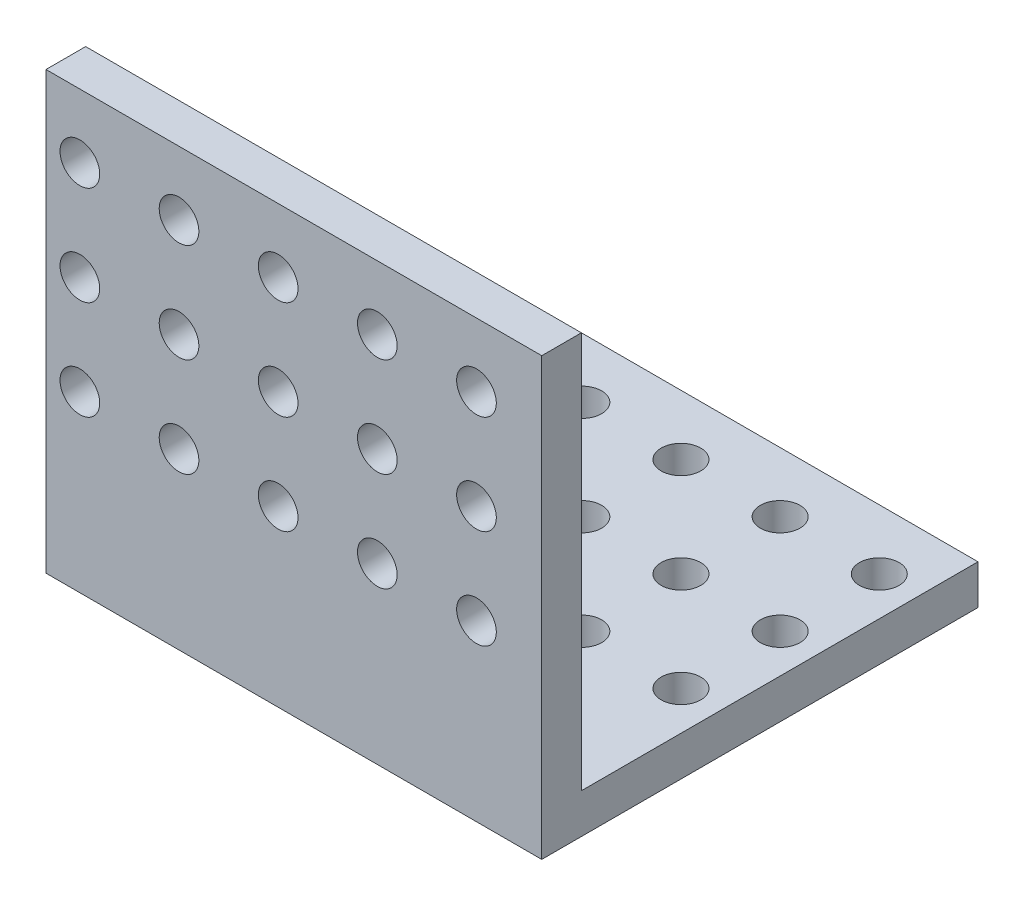
SolidWorks part; units mm, degrees
ref_plane "Front Plane" through (0, 0, 0) normal (0, 0, 1) x (1, 0, 0)
ref_plane "Top Plane" through (0, 0, 0) normal (0, 1, 0) x (1, 0, 0)
ref_plane "Right Plane" through (0, 0, 0) normal (1, 0, 0) x (0, 0, -1)
sketch "Sketch1" plane through (0, 0, 0) normal (1, 0, 0) x (0, 0, -1)
  line L0 (0, 40) -> (0, 0)
  line L1 (0, 0) -> (40, 0)
  dimension "D1" = 40
  dimension "D2" = 40
extrude "Extrude-Thin1" add sketch "Sketch1" along normal mid plane 50 thin
sketch "Sketch2" plane through (0, 0, 0) normal (0, 1, 0) x (1, 0, 0)
  circle A0 centre (-18.9109, 33.9533) radius 2
  circle A1 centre (-8.9109, 33.9533) radius 2
  circle A2 centre (1.0891, 33.9533) radius 2
  circle A3 centre (11.0891, 33.9533) radius 2
  circle A4 centre (21.0891, 33.9533) radius 2
  circle A5 centre (-8.9109, 23.9533) radius 2
  circle A6 centre (1.0891, 23.9533) radius 2
  circle A7 centre (11.0891, 23.9533) radius 2
  circle A8 centre (21.0891, 23.9533) radius 2
  circle A9 centre (-8.9109, 13.9533) radius 2
  circle A10 centre (1.0891, 13.9533) radius 2
  circle A11 centre (11.0891, 13.9533) radius 2
  circle A12 centre (21.0891, 13.9533) radius 2
  circle A13 centre (-18.9109, 23.9533) radius 2
  circle A14 centre (-18.9109, 13.9533) radius 2
  dimension "D1" = 5
  dimension "D2" = 3
extrude "Cut-Extrude1" cut sketch "Sketch2" against normal through all
sketch "Sketch3" plane through (0, 0, 0) normal (0, 0, -1) x (-1, 0, 0)
  circle A0 centre (-18.4162, 33.5615) radius 2
  circle A1 centre (-8.4162, 33.5615) radius 2
  circle A2 centre (1.5838, 33.5615) radius 2
  circle A3 centre (11.5838, 33.5615) radius 2
  circle A4 centre (21.5838, 33.5615) radius 2
  circle A5 centre (-8.4162, 23.5615) radius 2
  circle A6 centre (1.5838, 23.5615) radius 2
  circle A7 centre (11.5838, 23.5615) radius 2
  circle A8 centre (21.5838, 23.5615) radius 2
  circle A9 centre (-8.4162, 13.5615) radius 2
  circle A10 centre (1.5838, 13.5615) radius 2
  circle A11 centre (11.5838, 13.5615) radius 2
  circle A12 centre (21.5838, 13.5615) radius 2
  circle A13 centre (-18.4162, 23.5615) radius 2
  circle A14 centre (-18.4162, 13.5615) radius 2
  dimension "D1" = 5
  dimension "D2" = 3
extrude "Cut-Extrude2" cut sketch "Sketch3" against normal through all
